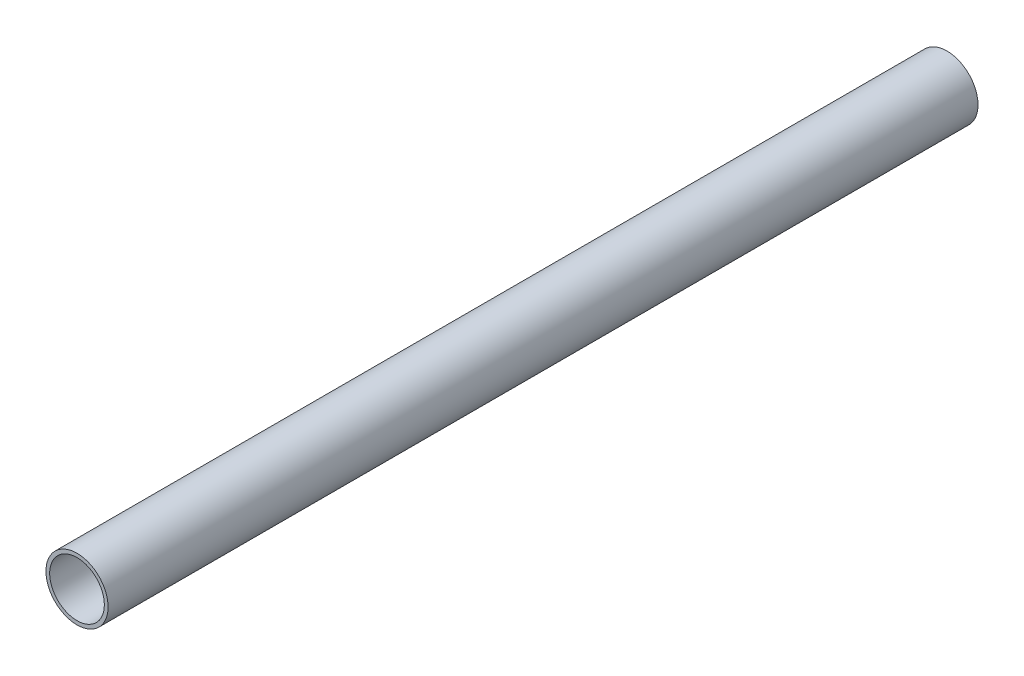
SolidWorks part; units mm, degrees
material "Carbon Fiber Tube - UD Approx"
ref_plane "Front Plane" through (0, 0, 0) normal (0, 0, 1) x (1, 0, 0)
ref_plane "Top Plane" through (0, 0, 0) normal (0, 1, 0) x (1, 0, 0)
ref_plane "Right Plane" through (0, 0, 0) normal (1, 0, 0) x (0, 0, -1)
sketch "Sketch1" plane through (0, 0, 0) normal (0, 0, 1) x (1, 0, 0)
  circle A0 centre (0, 0) radius 12.5
  circle A1 centre (0, 0) radius 11
  dimension "D1" = 25
  dimension "D2" = 22
extrude "Boss-Extrude1" add sketch "Sketch1" along normal blind 350
